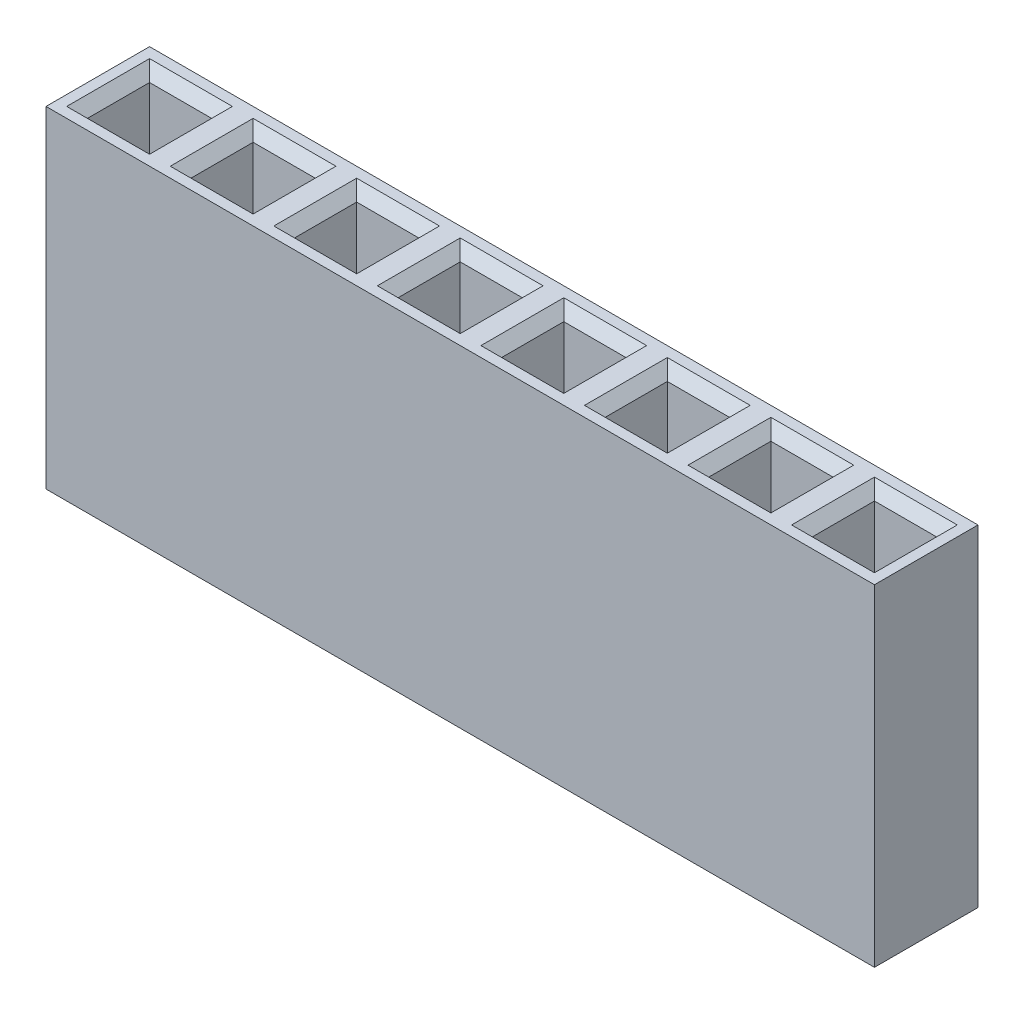
SolidWorks part; units mm, degrees
ref_plane "Front Plane" through (0, 0, 0) normal (0, 0, 1) x (1, 0, 0)
ref_plane "Top Plane" through (0, 0, 0) normal (0, 1, 0) x (1, 0, 0)
ref_plane "Right Plane" through (0, 0, 0) normal (1, 0, 0) x (0, 0, -1)
sketch "Sketch1" plane through (0, 0, 0) normal (0, 0, 1) x (1, 0, 0)
  line L1 (-1.25, -4) -> (1.25, -4)
  line L2 (-1.25, -4) -> (-1.25, 4)
  line L3 (-1.25, 4) -> (1.25, 4)
  line L4 (1.25, -4) -> (1.25, 4)
  line L5 (-1.25, -4) -> (1.25, 4) construction
  line L6 (-1.25, 4) -> (1.25, -4) construction
  point P0 (0, 0)
  dimension "D1" = 8
  dimension "D2" = 2.5
extrude "Boss-Extrude1" add sketch "Sketch1" along normal blind 2.5
sketch "Sketch2" plane through (0, 4, 0) normal (0, 1, 0) x (1, 0, 0)
  line L0 (0.75, -0.5) -> (-0.75, -0.5)
  line L1 (-0.75, -0.5) -> (-0.75, -2)
  line L2 (-0.75, -2) -> (0.75, -2)
  line L3 (0.75, -2) -> (0.75, -0.5)
  line L4 (1.25, 0) -> (-1.25, 0)
  line L5 (-1.25, 0) -> (-1.25, -2.5)
  line L6 (-1.25, -2.5) -> (1.25, -2.5)
  line L7 (1.25, -2.5) -> (1.25, 0)
  line L8 (1.25, 0) -> (-1.25, 0)
  line L9 (-1.25, 0) -> (-1.25, -2.5)
  line L10 (-1.25, -2.5) -> (1.25, -2.5)
  line L11 (1.25, -2.5) -> (1.25, 0)
  dimension "D1" = 0
  dimension "D2" = 0.5
extrude "Cut-Extrude2" cut sketch "Sketch2" against normal blind 7 contours L2 L3 L0 L1
chamfer "Chamfer3" distance 0.25 angle 45 4 edges at (0.75, 4, 1.25) (0, 4, 2) (-0.75, 4, 1.25) (0, 4, 0.5)
pattern_linear "LPattern2" count 8 spacing 2.5 along (1, 0, 0) of "Boss-Extrude1", "Cut-Extrude2", "Chamfer3"
